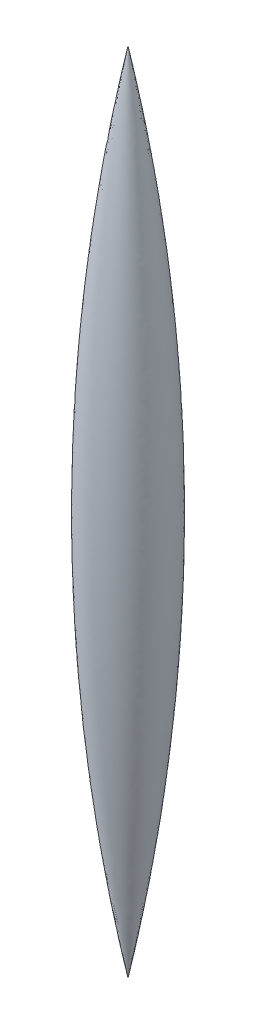
SolidWorks part; units mm, degrees
ref_plane "Front Plane" through (0, 0, 0) normal (0, 0, 1) x (1, 0, 0)
ref_plane "Top Plane" through (0, 0, 0) normal (0, 1, 0) x (1, 0, 0)
ref_plane "Right Plane" through (0, 0, 0) normal (1, 0, 0) x (0, 0, -1)
ref_plane "Plane1" through (0, 63.5, 0) normal (0, 1, 0) x (1, 0, 0)
ref_plane "Plane2" through (0, -63.5, 0) normal (0, 1, 0) x (1, 0, 0)
sketch "Sketch5" plane through (0, 0, 0) normal (0, 0, 1) x (1, 0, 0)
  line L0 (0, 63.5) -> (0, -63.5)
  arc A0 (0, 63.5) -> (0, -63.5) centre (-317.6866, 0) cw
  point P4 (0, 0)
revolve "Revolve1" add sketch "Sketch5" angle 360 about L0
